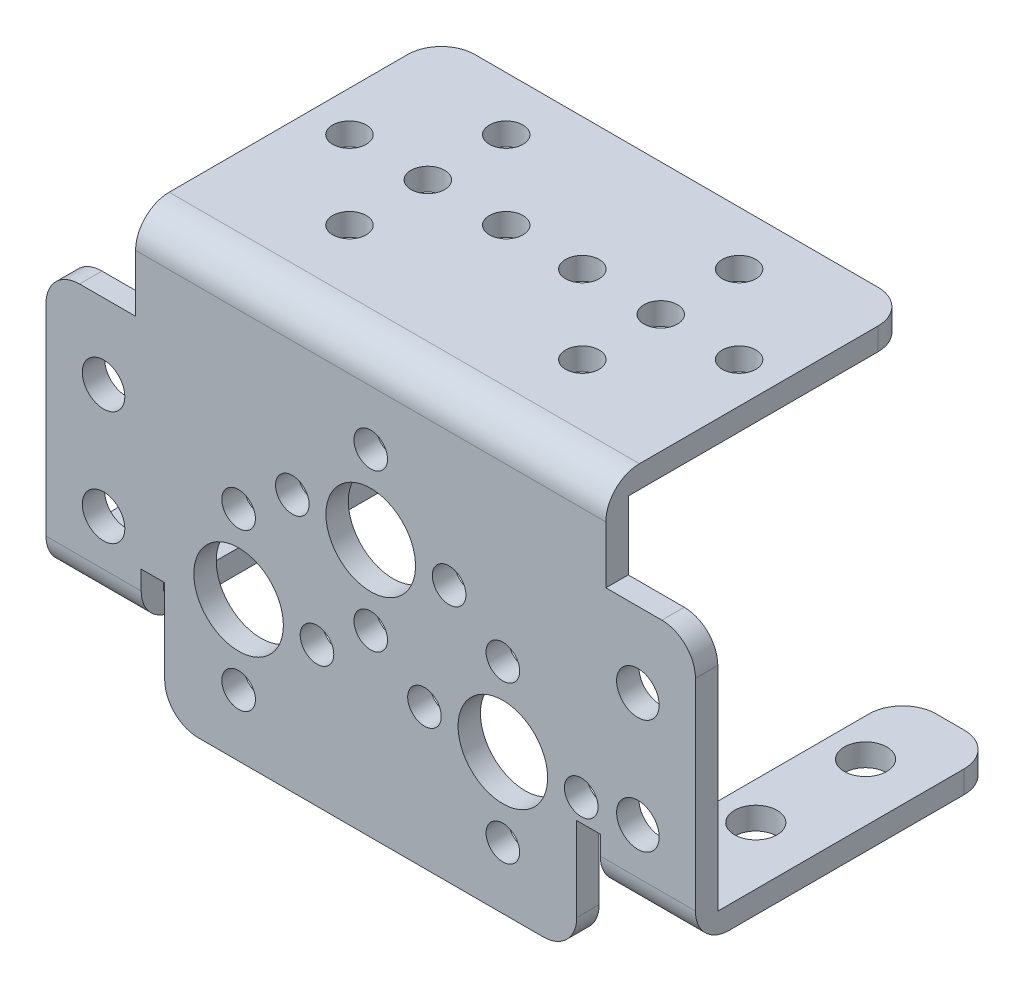
SolidWorks part; units mm, degrees
material "1060 合金"
ref_plane "前视基准面" through (0, 0, 0) normal (0, 0, 1) x (1, 0, 0)
ref_plane "上视基准面" through (0, 0, 0) normal (0, 1, 0) x (1, 0, 0)
ref_plane "右视基准面" through (0, 0, 0) normal (1, 0, 0) x (0, 0, -1)
sketch "草图1" plane through (0, 0, 0) normal (0, 0, 1) x (1, 0, 0)
  line L0 (0, 0) -> (42, 0)
  line L1 (42, -8.1) -> (42, 0)
  line L2 (42, -8.1) -> (50, -8.1)
  line L3 (50, -8.1) -> (50, -32.1)
  line L4 (50, -32.1) -> (41.5, -32.1)
  line L5 (41.5, -32.1) -> (41.5, -27.4)
  line L6 (41.5, -27.4) -> (39.4, -27.4)
  line L7 (39.4, -27.4) -> (39.4, -37.9)
  line L8 (39.4, -37.9) -> (2.6, -37.9)
  line L9 (21, 6.0181) -> (21, -43.2428) construction
  line L10 (2.6, -27.4) -> (2.6, -37.9)
  line L11 (0.5, -27.4) -> (2.6, -27.4)
  line L12 (0.5, -32.1) -> (0.5, -27.4)
  line L13 (-8, -32.1) -> (0.5, -32.1)
  line L14 (-8, -8.1) -> (-8, -32.1)
  line L15 (0, -8.1) -> (-8, -8.1)
  line L16 (0, -8.1) -> (0, 0)
  point P14 (21, -37.9)
  point P21 (21, 0)
  dimension "D1" = 8.1
  dimension "D2" = 42
  dimension "D3" = 8
  dimension "D4" = 24
  dimension "D5" = 8.5
  dimension "D6" = 2.1
  dimension "D7" = 4.7
  dimension "D8" = 10.5
extrude "凸台-拉伸1" add sketch "草图1" along normal blind 2
sketch "草图2" plane through (0, 0, 0) normal (0, 0, -1) x (-1, 0, 0)
  line L0 (0, 0) -> (0, -8.1) construction
  line L1 (-42, 0) -> (0, 0)
  line L2 (-42, 0) -> (-42, -2)
  line L3 (-42, -2) -> (0, -2)
  line L4 (0, 0) -> (0, -2)
  dimension "D1" = 2
extrude "凸台-拉伸2" add sketch "草图2" along normal blind 25.3
sketch "草图3" plane through (0, 0, 0) normal (0, 0, -1) x (-1, 0, 0)
  line L0 (-41.5, -27.4) -> (-41.5, -32.1) construction
  line L1 (-50, -32.1) -> (-41.5, -32.1)
  line L2 (-50, -32.1) -> (-50, -30.1)
  line L3 (-50, -30.1) -> (-41.5, -30.1)
  line L4 (-41.5, -32.1) -> (-41.5, -30.1)
  line L5 (8, -8.1) -> (8, -32.1) construction
  line L6 (-0.5, -32.1) -> (8, -32.1)
  line L7 (-0.5, -32.1) -> (-0.5, -30.1)
  line L8 (-0.5, -30.1) -> (8, -30.1)
  line L9 (8, -32.1) -> (8, -30.1)
  dimension "D1" = 2
  dimension "D2" = 2
extrude "凸台-拉伸3" add sketch "草图3" along normal blind 25
fillet "圆角3" radius 3 1 edges at (42, -1, -25.3)
fillet "圆角4" radius 3 1 edges at (41.5, -31.1, -25)
fillet "圆角5" radius 3 1 edges at (0, -1, -25.3)
fillet "圆角6" radius 3 1 edges at (50, -31.1, -25)
fillet "圆角7" radius 3 1 edges at (-8, -31.1, -25)
fillet "圆角8" radius 3 1 edges at (0.5, -31.1, -25)
fillet "圆角9" radius 3 1 edges at (39.4, -37.9, 1)
fillet "圆角10" radius 3 1 edges at (2.6, -37.9, 1)
fillet "圆角11" radius 3 1 edges at (50, -8.1, 1)
fillet "圆角12" radius 3 1 edges at (-8, -8.1, 1)
ref_plane "基准面1" through (21, 0, 0) normal (1, 0, 0) x (0, 0, -1)
sketch "草图5" plane through (0, 0, 0) normal (0, 0, -1) x (-1, 0, 0)
  line L1 (-21, 11.55) -> (-21, -11.55) construction
  circle A2 centre (-32.8, -32.4) radius 1.5
  circle A5 centre (-32.8, -25.4) radius 4
  circle A6 centre (-25.8, -25.4) radius 1.5
  circle A7 centre (-32.8, -18.4) radius 1.5
  circle A8 centre (-39.8, -25.4) radius 1.5
  circle A12 centre (-21, -14.9) radius 4
  circle A14 centre (-14, -14.9) radius 1.5
  circle A15 centre (-21, -7.9) radius 1.5
  circle A16 centre (-21, -21.9) radius 1.5
  circle A17 centre (-44.86, -25) radius 1.9
  circle A18 centre (-44.86, -14.8) radius 1.9
  circle A19 centre (-28, -14.9) radius 1.5
  circle A20 centre (-9.2, -32.4) radius 1.5
  circle A21 centre (-9.2, -18.4) radius 1.5
  circle A22 centre (-16.2, -25.4) radius 1.5
  circle A23 centre (-2.2, -25.4) radius 1.5
  circle A24 centre (-9.2, -25.4) radius 4
  circle A25 centre (2.86, -25) radius 1.9
  circle A26 centre (2.86, -14.8) radius 1.9
  point P28 (-32.8, -25.4)
  dimension "D6" = 4
  dimension "D1" = 47.72
  dimension "D2" = 23.86
  dimension "D3" = 10.2
extrude "切除-拉伸5" cut sketch "草图5" against normal blind 2 contours A18 | A17 | A5 | A7 | A19 | A12 | A15 | A14 | A21 | A26 | A25 | A24 | A20 | A22 | A6 | A16 | A2 | A8
sketch "草图9" plane through (0, -30.1, 0) normal (0, 1, 0) x (1, 0, 0)
  line L0 (34.6227, 18.34) -> (58.7301, 18.34)
  line L1 (44.85, 31.6584) -> (44.85, -9.7774)
  line L2 (34.6227, 8.54) -> (59.8815, 8.54)
  line L3 (20.85, 27.7662) -> (20.85, -8.1121)
  line L4 (41.5, -2) -> (50, -2) construction
  line L7 (39, 25.3) -> (3, 25.3)
  line L8 (0, 22.3) -> (0, -2)
  line L9 (0, -2) -> (42, -2)
  line L10 (42, -2) -> (42, 22.3)
  line L11 (39, 25.3) -> (3, 25.3)
  line L12 (0, 22.3) -> (0, -2)
  line L13 (0, -2) -> (42, -2)
  line L14 (42, -2) -> (42, 22.3)
  circle A0 centre (44.85, 18.34) radius 1.9
  circle A1 centre (44.85, 8.54) radius 1.9
  circle A2 centre (-3.15, 8.54) radius 1.9
  circle A3 centre (-3.15, 18.34) radius 1.9
  arc A4 (3, 25.3) -> (0, 22.3) centre (3, 22.3) ccw
  arc A5 (42, 22.3) -> (39, 25.3) centre (39, 22.3) ccw
  arc A6 (3, 25.3) -> (0, 22.3) centre (3, 22.3) ccw
  arc A7 (42, 22.3) -> (39, 25.3) centre (39, 22.3) ccw
  dimension "D4" = 0
  dimension "D5" = 10.54
  dimension "D1" = 48
  dimension "D2" = 5.15
  dimension "D3" = 9.8
extrude "切除-拉伸6" cut sketch "草图9" against normal blind 2 contours A3 | A2 | A0 | A1
sketch "草图10" plane through (0, -2, 0) normal (0, -1, 0) x (1, 0, 0)
  line L0 (-15.7056, -20.5) -> (58.7463, -20.5)
  line L1 (-17.6923, -13.5) -> (56.665, -13.5)
  line L2 (-16.5571, -6.5) -> (57.7056, -6.5)
  line L3 (10.6, 10.7234) -> (10.6, -31.6584)
  line L5 (21, -29.3895) -> (21, 5.0117)
  line L9 (0, 0) -> (0, -22.3)
  line L10 (3, -25.3) -> (39, -25.3)
  line L11 (42, -22.3) -> (42, 0)
  line L12 (42, 0) -> (0, 0)
  line L13 (0, 0) -> (0, -22.3)
  line L14 (3, -25.3) -> (39, -25.3)
  line L15 (42, -22.3) -> (42, 0)
  line L16 (42, 0) -> (0, 0)
  circle A0 centre (10.6, -20.5) radius 1.5
  circle A1 centre (10.6, -13.5) radius 1.5
  circle A2 centre (10.6, -6.5) radius 1.5
  circle A3 centre (17.6, -13.5) radius 1.5
  circle A4 centre (10.6, -20.5) radius 1.5
  circle A5 centre (3.6, -13.5) radius 1.5
  circle A6 centre (31.4, -20.5) radius 1.5
  circle A7 centre (24.4, -13.5) radius 1.5
  arc A8 (0, -22.3) -> (3, -25.3) centre (3, -22.3) ccw
  arc A9 (39, -25.3) -> (42, -22.3) centre (39, -22.3) ccw
  arc A10 (0, -22.3) -> (3, -25.3) centre (3, -22.3) ccw
  arc A11 (39, -25.3) -> (42, -22.3) centre (39, -22.3) ccw
  circle A12 centre (31.4, -13.5) radius 1.5
  circle A13 centre (38.4, -13.5) radius 1.5
  circle A14 centre (31.4, -6.5) radius 1.5
  point P26 (10.6, -13.5)
  dimension "D5" = 4
  dimension "D1" = 4.5
  dimension "D2" = 7
  dimension "D3" = 7
  dimension "D4" = 10.6
  dimension "D6" = 0
extrude "切除-拉伸7" cut sketch "草图10" against normal blind 2 contours A2 | A1 | A3 | A0 | A5 | A7 | A14 | A12 | A6 | A13
fillet "圆角13" radius 3 1 edges at (21, 0, 2)
fillet "圆角14" radius 3 1 edges at (45.75, -32.1, 2)
fillet "圆角15" radius 3 1 edges at (-3.75, -32.1, 2)
